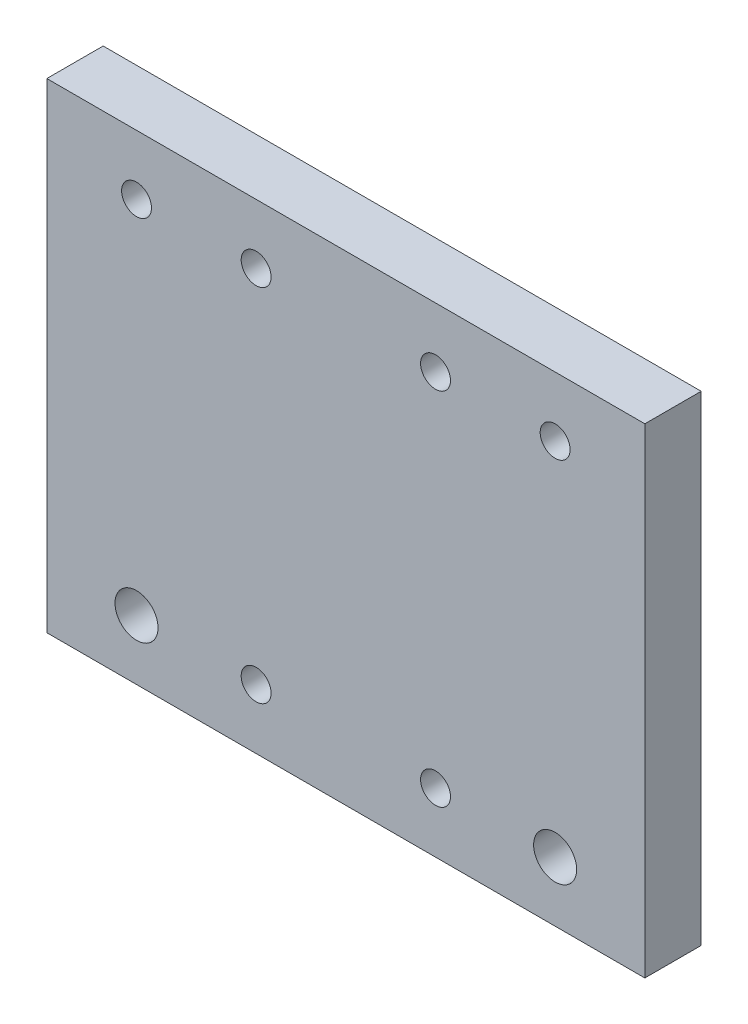
SolidWorks part; units mm, degrees
ref_plane "Front Plane" through (0, 0, 0) normal (0, 0, 1) x (1, 0, 0)
ref_plane "Top Plane" through (0, 0, 0) normal (0, 1, 0) x (1, 0, 0)
ref_plane "Right Plane" through (0, 0, 0) normal (1, 0, 0) x (0, 0, -1)
sketch "Sketch1" plane through (0, 0, 0) normal (0, 0, 1) x (1, 0, 0)
  line L0 (17.7107, -15.3074) -> (87.7107, -15.3074) construction
  line L1 (17.7107, -15.3074) -> (17.7107, 44.9526) construction
  line L2 (17.7107, 44.9526) -> (87.7107, 44.9526) construction
  line L3 (87.7107, -15.3074) -> (87.7107, 44.9526) construction
  line L4 (17.7107, -15.3074) -> (87.7107, 44.9526) construction
  line L5 (17.7107, 44.9526) -> (87.7107, -15.3074) construction
  line L6 (2.7107, -25.3074) -> (102.7107, -25.3074)
  line L7 (2.7107, -25.3074) -> (2.7107, 54.9526)
  line L8 (2.7107, 54.9526) -> (102.7107, 54.9526)
  line L9 (102.7107, -25.3074) -> (102.7107, 54.9526)
  line L10 (2.7107, -25.3074) -> (102.7107, 54.9526) construction
  line L11 (2.7107, 54.9526) -> (102.7107, -25.3074) construction
  circle A0 centre (17.7107, -15.3074) radius 3.6
  circle A1 centre (17.7107, 44.9526) radius 2.5
  circle A2 centre (87.7107, 44.9526) radius 2.5
  circle A3 centre (87.7107, -15.3074) radius 3.6
  point P5 (52.7107, 14.8226)
  point P13 (52.7107, 14.8226)
  dimension "D1" = 7.2
  dimension "D3" = 5
  dimension "D2" = 60.26
  dimension "D4" = 70
  dimension "D5" = 15
  dimension "D6" = 15
  dimension "D7" = 10
  dimension "D8" = 10
extrude "Boss-Extrude1" add sketch "Sketch1" along normal blind 9.42
sketch "Sketch2" plane through (0, 0, 9.42) normal (0, 0, 1) x (1, 0, 0)
  line L0 (52.7107, -15.3074) -> (52.7107, -25.3074) construction
  line L1 (37.7107, -15.3074) -> (67.7107, -15.3074) construction
  line L2 (37.7107, -15.3074) -> (37.7107, 44.9526) construction
  line L3 (37.7107, 44.9526) -> (67.7107, 44.9526) construction
  line L4 (67.7107, -15.3074) -> (67.7107, 44.9526) construction
  line L5 (37.7107, -15.3074) -> (67.7107, 44.9526) construction
  line L6 (37.7107, 44.9526) -> (67.7107, -15.3074) construction
  line L7 (2.7107, -25.3074) -> (102.7107, -25.3074) construction
  line L8 (52.7107, 44.9526) -> (52.7107, 54.9526) construction
  line L9 (102.7107, 54.9526) -> (2.7107, 54.9526) construction
  line L10 (2.7107, 54.9526) -> (2.7107, -25.3074) construction
  circle A0 centre (37.7107, -15.3074) radius 2.5
  circle A1 centre (67.7107, -15.3074) radius 2.5
  circle A2 centre (67.7107, 44.9526) radius 2.5
  circle A3 centre (37.7107, 44.9526) radius 2.5
  point P4 (52.7107, 14.8226)
  dimension "D1" = 5
  dimension "D2" = 5
  dimension "D3" = 5
  dimension "D4" = 5
  dimension "D5" = 10
  dimension "D6" = 35
extrude "Cut-Extrude1" cut sketch "Sketch2" against normal through all
